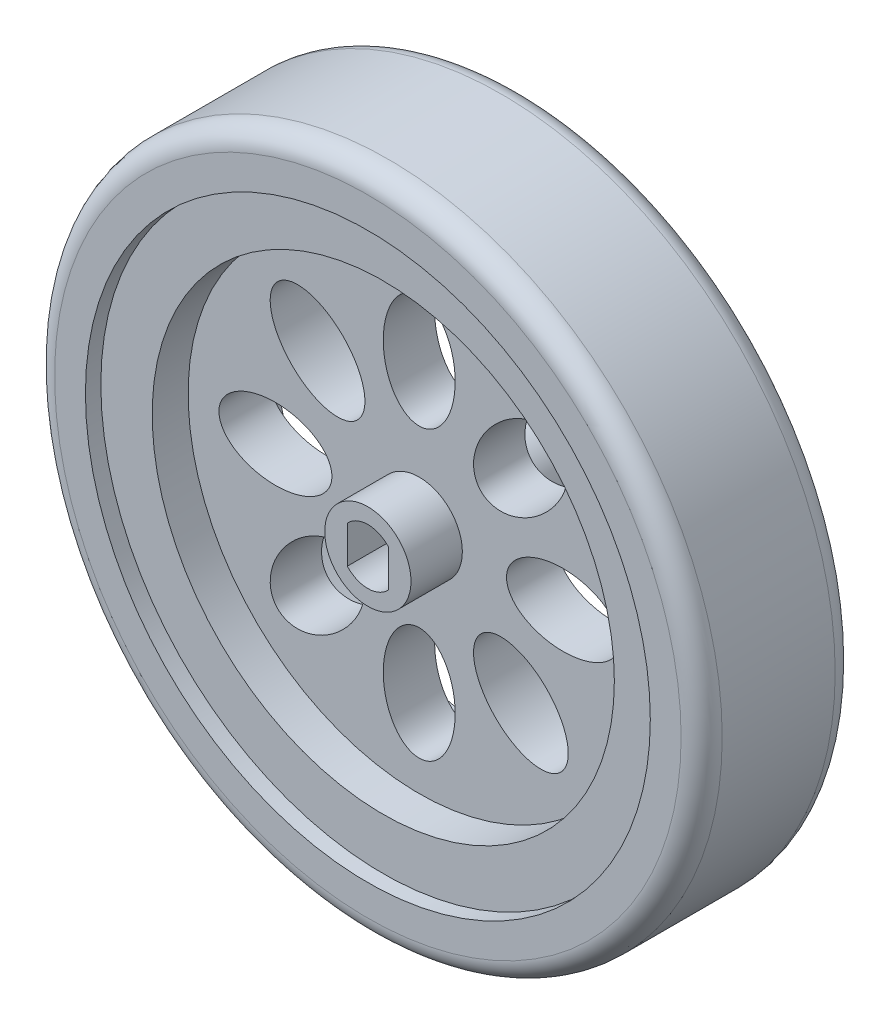
SolidWorks part; units mm, degrees
ref_plane "Front Plane" through (0, 0, 0) normal (0, 0, 1) x (1, 0, 0)
ref_plane "Top Plane" through (0, 0, 0) normal (0, 1, 0) x (1, 0, 0)
ref_plane "Right Plane" through (0, 0, 0) normal (1, 0, 0) x (0, 0, -1)
sketch "Sketch1" plane through (0, 0, 0) normal (0, 0, 1) x (1, 0, 0)
  circle A0 centre (0, 0) radius 32.5
  circle A1 centre (0, 0) radius 27.5
  dimension "D1" = 65
  dimension "D2" = 55
extrude "Boss-Extrude1" add sketch "Sketch1" along normal mid plane 15
fillet "Fillet1" radius 2 2 edges at (32.5, 0, -7.5) (32.5, 0, 7.5)
sketch "Sketch3" plane through (0, 0, 7.5) normal (0, 0, 1) x (1, 0, 0)
  line L0 (-2, 1.8138) -> (-2, -1.8138)
  line L1 (2, 1.8138) -> (2, -1.8138)
  circle A0 centre (0, 0) radius 4.2
  arc A1 (-2, -1.8138) -> (2, -1.8138) centre (0, 0) ccw
  arc A2 (2, 1.8138) -> (-2, 1.8138) centre (0, 0) ccw
  dimension "D1" = 5.4
  dimension "D4" = 8.4
  dimension "D2" = 2
  dimension "D3" = 2
extrude "Boss-Extrude2" add sketch "Sketch3" against normal offset from surface (18.85 mm away) 3.85 separate body up to face at (30.5, 0, -7.5) offset beyond the face yes
sketch "Sketch4" plane through (0, 0, 0) normal (0, 0, 1) x (1, 0, 0)
  circle A0 centre (0, 0) radius 27.5
  circle A1 centre (0, 0) radius 27.5 construction
  circle A2 centre (0, 0) radius 22.5
  dimension "D1" = 5
extrude "Boss-Extrude3" add sketch "Sketch4" along normal mid plane 12
sketch "Sketch5" plane through (0, 0, 0) normal (0, 0, 1) x (1, 0, 0)
  circle A0 centre (0, 0) radius 22.5
  circle A1 centre (0, 0) radius 4.2
  circle A2 centre (0, 0) radius 22.5 construction
  circle A3 centre (0, 0) radius 4.2 construction
extrude "Boss-Extrude4" add sketch "Sketch5" along normal mid plane 5
sketch "Sketch7" plane through (0, 0, 0) normal (0, 0, 1) x (1, 0, 0)
  ellipse E0 centre (0, 14) end of major axis (0, 19.5) minor radius 3.5
  point P1 (0, 0)
  point P7 (0, 0)
  point P8 (-0.9091, 14.7046)
  point P9 (0, 0)
  point P10 (0, 0)
  point P12 (0, 19.2007)
  point P13 (0, 12.981)
  dimension "D1" = 11
  dimension "D2" = 7
  dimension "D3" = 14
extrude "Cut-Extrude1" cut sketch "Sketch7" against normal through all both and the other way through all
pattern_circular "CirPattern1" count 8 over 360 about axis through (0, 0, 6) along (0, 0, -1) of "Cut-Extrude1"
